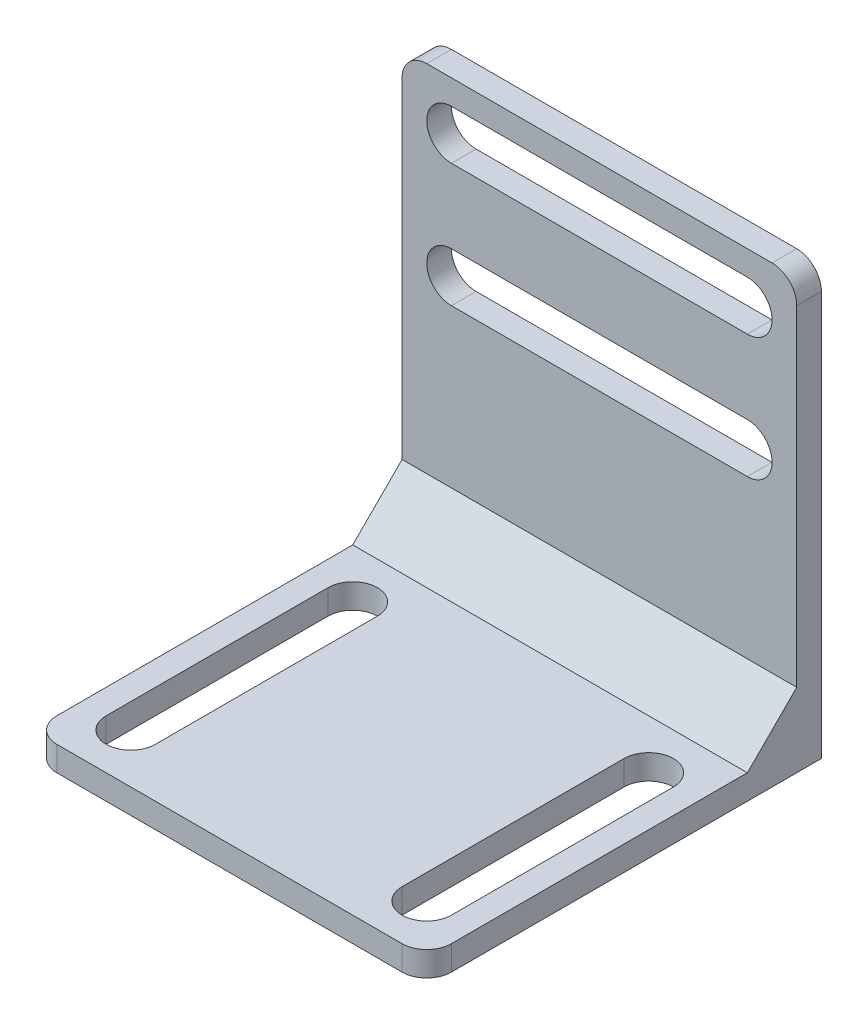
SolidWorks part; units mm, degrees
ref_plane "Front" through (0, 0, 0) normal (0, 0, 1) x (1, 0, 0)
ref_plane "Top" through (0, 0, 0) normal (0, 1, 0) x (1, 0, 0)
ref_plane "Right" through (0, 0, 0) normal (1, 0, 0) x (0, 0, -1)
sketch "Sketch1" plane through (0, 0, 0) normal (0, 1, 0) x (1, 0, 0)
  line L1 (-40, 40) -> (40, 40)
  line L2 (-40, 40) -> (-40, -40)
  line L3 (-40, -40) -> (40, -40)
  line L4 (40, 40) -> (40, -40)
  line L5 (-40, 40) -> (40, -40) construction
  line L6 (-40, -40) -> (40, 40) construction
  point P0 (0, 0)
  dimension "D1" = 80
extrude "Boss-Extrude1" add sketch "Sketch1" along normal blind 5
sketch "Sketch2" plane through (0, 5, 0) normal (0, 1, 0) x (1, 0, 0)
  line L0 (40, -40) -> (40, 40) construction
  line L1 (-40, 40) -> (40, 40)
  line L2 (-40, 40) -> (-40, 35)
  line L3 (-40, 35) -> (40, 35)
  line L4 (40, 40) -> (40, 35)
  dimension "D1" = 5
extrude "Boss-Extrude2" add sketch "Sketch2" along normal blind 82
sketch "Sketch4" plane through (40, 0, 0) normal (1, 0, 0) x (0, 0, -1)
  line L0 (25, 5) -> (35, 15)
  line L1 (-40, 5) -> (35, 5) construction
  line L2 (35, 87) -> (35, 5) construction
  dimension "D1" = 10
  dimension "D2" = 45
sketch "Sketch5" plane through (-40, 0, 0) normal (-1, 0, 0) x (0, 0, 1)
  line L0 (-25, 5) -> (-35, 15) construction
  line L1 (-25, 5) -> (-35, 15)
rib "Rib5" [suppressed] sketch "Sketch4" sketch "Sketch4" thickness 5 extrusion direction parallel to sketch draft on no parameters "D1"=5
rib "Rib6" [suppressed] sketch "Sketch5" sketch "Sketch5" thickness 5 extrusion direction parallel to sketch draft on no parameters "D1"=5
sketch "Sketch6" plane through (0, 0, -40) normal (0, 0, -1) x (-1, 0, 0)
  line L0 (-30, 77) -> (30, 77) construction
  line L1 (-30, 82) -> (30, 82)
  line L2 (-30, 72) -> (30, 72)
  line L3 (-30, 52) -> (30, 52) construction
  line L4 (-30, 57) -> (30, 57)
  line L5 (-30, 47) -> (30, 47)
  line L6 (-40, 87) -> (40, 87) construction
  arc A0 (-30, 82) -> (-30, 72) centre (-30, 77) ccw
  arc A1 (30, 72) -> (30, 82) centre (30, 77) ccw
  arc A2 (-30, 57) -> (-30, 47) centre (-30, 52) ccw
  arc A3 (30, 47) -> (30, 57) centre (30, 52) ccw
  point P2 (0, 77)
  point P7 (0, 52)
  point P17 (0, 87)
  dimension "D1" = 5
  dimension "D2" = 10
  dimension "D3" = 60
  dimension "D4" = 25
extrude "Cut-Extrude1" cut sketch "Sketch6" against normal through all
sketch "Sketch7" plane through (0, 5, 0) normal (0, 1, 0) x (1, 0, 0)
  line L0 (-30, -30) -> (-30, 15) construction
  line L1 (-35, -30) -> (-35, 15)
  line L2 (-25, -30) -> (-25, 15)
  line L3 (30, 15) -> (30, -30) construction
  line L4 (35, 15) -> (35, -30)
  line L5 (25, 15) -> (25, -30)
  line L9 (-40, -40) -> (40, -40) construction
  arc A0 (-35, -30) -> (-25, -30) centre (-30, -30) ccw
  arc A1 (-25, 15) -> (-35, 15) centre (-30, 15) ccw
  arc A2 (35, 15) -> (25, 15) centre (30, 15) ccw
  arc A3 (25, -30) -> (35, -30) centre (30, -30) ccw
  point P2 (-30, -7.5)
  point P7 (30, -7.5)
  dimension "D1" = 5
  dimension "D5" = 45
  dimension "D2" = 30
  dimension "D3" = 30
  dimension "D4" = 10
extrude "Cut-Extrude2" cut sketch "Sketch7" against normal through all
fillet "Fillet1" radius 5 2 edges at (-40, 2.5, 40) (40, 2.5, 40)
fillet "Fillet2" radius 5 2 edges at (-40, 87, -37.5) (40, 87, -37.5)
sketch "Sketch8" plane through (40, 0, 0) normal (1, 0, 0) x (0, 0, -1)
  line L0 (25, 5) -> (35, 15) construction
  line L1 (25, 5) -> (35, 15)
  line L2 (-35, 5) -> (35, 5) construction
  line L3 (35, 82) -> (35, 5) construction
  line L4 (-35, 5) -> (35, 5)
  line L5 (35, 82) -> (35, 5)
  line M3 (35, 82) -> (35, 5)
  line M4 (35, 5) -> (-35, 5)
extrude "Boss-Extrude3" add sketch "Sketch8" against normal up to surface (80 mm away) contours L1 M4 M3 up to face at (-40, 29, -13.3333)
equation "\"D3@Sketch7\"=\"D2@Sketch7\""
